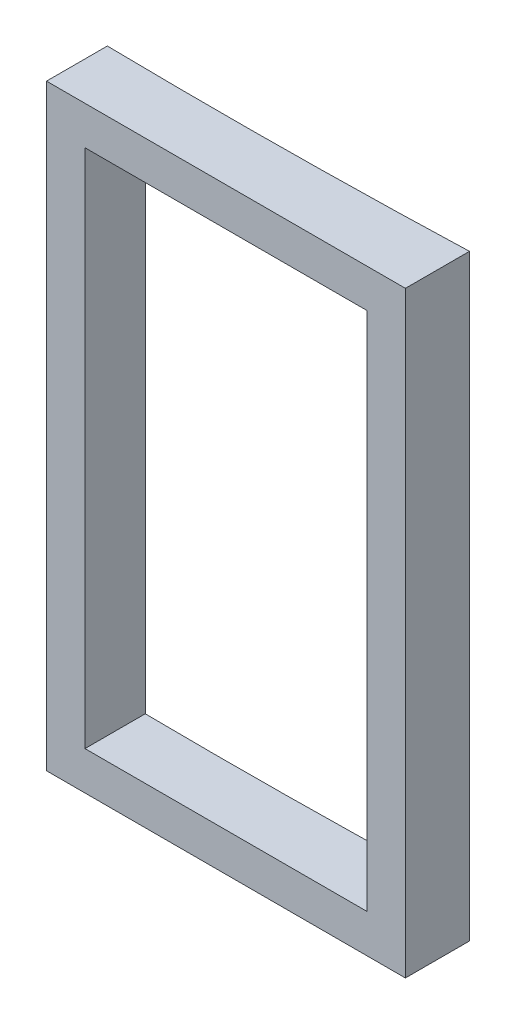
SolidWorks part; units mm, degrees
ref_plane "Front Plane" through (0, 0, 0) normal (0, 0, 1) x (1, 0, 0)
ref_plane "Top Plane" through (0, 0, 0) normal (0, 1, 0) x (1, 0, 0)
ref_plane "Right Plane" through (0, 0, 0) normal (1, 0, 0) x (0, 0, -1)
sketch "Sketch2" plane through (0, 0, 0) normal (0, 1, 0) x (1, 0, 0)
  line L0 (-6692.1861, -5017.368) -> (-6692.1861, -5267.368)
  line L1 (-8092.1861, -5030.0999) -> (-8092.1861, -5267.368)
  line L2 (-8092.1861, -5267.368) -> (-6692.1861, -5267.368)
  arc A0 (-6692.1861, -5017.368) -> (-8092.1861, -5030.0999) centre (-7642.1861, 22466.218) cw
  dimension "D1" = 27500
  dimension "D2" = 1400
  dimension "D3" = 250
extrude "Boss-Extrude1" add sketch "Sketch2" along normal blind 2330
sketch "Sketch3" plane through (0, 0, 5267.368) normal (0, 0, 1) x (1, 0, 0)
  line L0 (-7942.1861, 2180) -> (-6842.1861, 2180)
  line L1 (-6842.1861, 2180) -> (-6842.1861, 150)
  line L2 (-6842.1861, 150) -> (-7942.1861, 150)
  line L3 (-7942.1861, 150) -> (-7942.1861, 2180)
  line L4 (-6692.1861, 2330) -> (-6692.1861, 0) construction
  line L5 (-8092.1861, 0) -> (-6692.1861, 0) construction
  line L6 (-8092.1861, 2330) -> (-6692.1861, 2330) construction
  point P3 (-7392.1861, 2180)
  dimension "D1" = 1100
  dimension "D2" = 150
  dimension "D3" = 150
  dimension "D4" = 150
  dimension "D5" = 2030
extrude "Cut-Extrude1" cut sketch "Sketch3" against normal blind 3000
